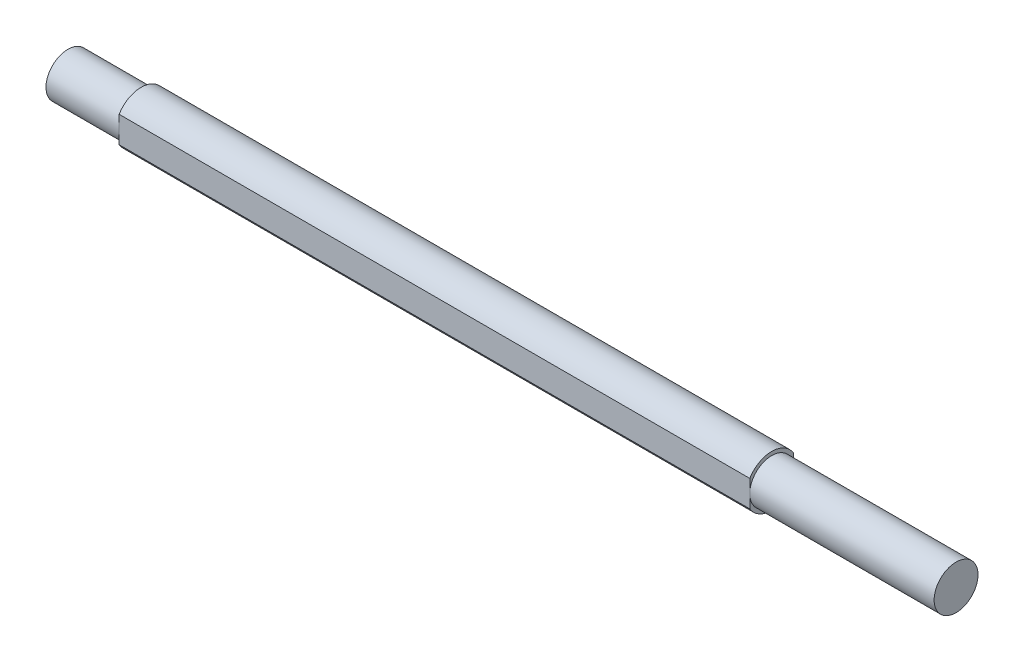
SolidWorks part; units mm, degrees
ref_plane "Front Plane" through (0, 0, 0) normal (0, 0, 1) x (1, 0, 0)
ref_plane "Top Plane" through (0, 0, 0) normal (0, 1, 0) x (1, 0, 0)
ref_plane "Right Plane" through (0, 0, 0) normal (1, 0, 0) x (0, 0, -1)
sketch "Çizim1" plane through (0, 0, 0) normal (0, 0, 1) x (1, 0, 0)
  line L0 (-303.5, 0) -> (303.5, 0)
  line L1 (-303.5, 0) -> (-303.5, 15)
  line L2 (-303.5, 15) -> (-253.5, 15)
  line L3 (-253.5, 15) -> (-253.5, 17.5)
  line L4 (-253.5, 17.5) -> (177.5, 17.5)
  line L5 (177.5, 17.5) -> (177.5, 15)
  line L6 (177.5, 15) -> (303.5, 15)
  line L7 (303.5, 15) -> (303.5, 0)
  point P4 (0, 0)
  dimension "D1" = 50
  dimension "D2" = 15
  dimension "D3" = 431
  dimension "D4" = 126
  dimension "D5" = 17.5
revolve "Döndür1" add sketch "Çizim1" angle 360 about L0
sketch "Çizim2" plane through (-253.5, 0, 0) normal (-1, 0, 0) x (0, 0, 1)
  line L0 (-15, 9.0139) -> (-15, -9.0139)
  line L1 (0, 0) -> (0, 4.7116) construction
  line L2 (15, 9.0139) -> (15, -9.0139)
  circle A2 centre (0, 0) radius 17.5 construction
  arc A3 (-15, 9.0139) -> (-15, -9.0139) centre (0, 0) ccw
  circle A4 centre (0, 0) radius 15 construction
  arc A5 (15, 9.0139) -> (15, -9.0139) centre (0, 0) cw
  point P3 (-15, 0)
extrude "Kes-Ekstrüzyon1" cut sketch "Çizim2" against normal up to surface (431 mm away) up to face at (177.5, -17.5, 0)
sketch "Çizim3" plane through (0, 0, 0) normal (0, 1, 0) x (1, 0, 0)
  line L0 (297.5, 0) -> (237.5, 0) construction
  line L1 (297.5, -4) -> (237.5, -4)
  line L2 (297.5, 4) -> (237.5, 4)
  line L3 (303.5, -15) -> (303.5, 15) construction
  arc A0 (297.5, -4) -> (297.5, 4) centre (297.5, 0) ccw
  arc A1 (237.5, 4) -> (237.5, -4) centre (237.5, 0) ccw
  point P3 (267.5, 0)
  dimension "D1" = 8
  dimension "D2" = 6
  dimension "D3" = 60
extrude "Kes-Ekstrüzyon2" cut sketch "Çizim3" against normal blind 24
